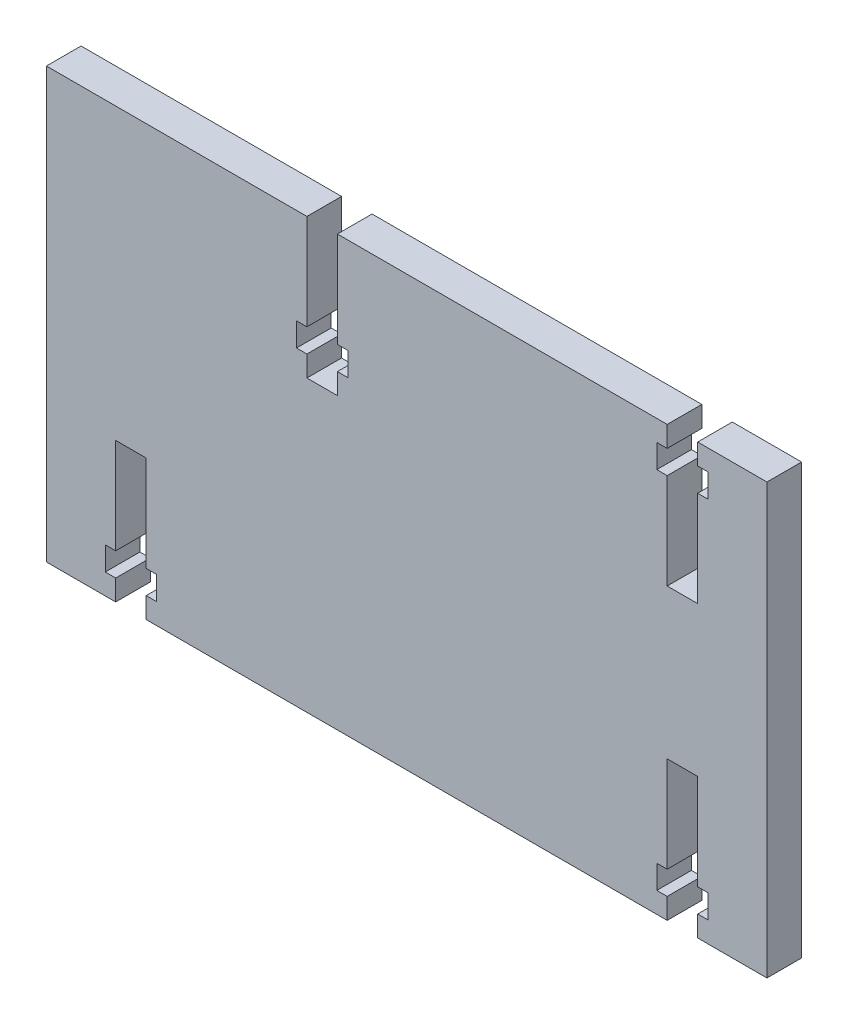
SolidWorks part; units mm, degrees
ref_plane "Front Plane" through (0, 0, 0) normal (0, 0, 1) x (1, 0, 0)
ref_plane "Top Plane" through (0, 0, 0) normal (0, 1, 0) x (1, 0, 0)
ref_plane "Right Plane" through (0, 0, 0) normal (1, 0, 0) x (0, 0, -1)
sketch "Sketch1" plane through (0, 0, 0) normal (0, 0, 1) x (1, 0, 0)
  line L1 (-52, 31) -> (52, 31)
  line L2 (-52, 31) -> (-52, -31)
  line L3 (-52, -31) -> (52, -31)
  line L4 (52, 31) -> (52, -31)
  dimension "D1" = 104
  dimension "D2" = 62
  dimension "D3" = 31
  dimension "D4" = 52
extrude "Boss-Extrude1" add sketch "Sketch1" along normal blind 5
sketch "Sketch2" plane through (0, 0, 0) normal (0, 0, -1) x (-1, 0, 0)
  line L0 (-39.8, -31) -> (-39.8, -16.1548) construction
  line L1 (-37.6, -28) -> (-37.6, -31)
  line L2 (-42, -24.6) -> (-42, -10.8)
  line L3 (-36.1, -24.6) -> (-37.6, -24.6)
  line L4 (-36.1, -28) -> (-36.1, -24.6)
  line L5 (-37.6, -28) -> (-36.1, -28)
  line L6 (-43.5, -24.6) -> (-42, -24.6)
  line L7 (-43.5, -28) -> (-43.5, -24.6)
  line L8 (-42, -28) -> (-43.5, -28)
  line L9 (-42, -31) -> (-37.6, -31)
  line L10 (-37.6, -10.8) -> (-37.6, -24.6)
  line L11 (-42, -10.8) -> (-37.6, -10.8)
  line L12 (-42, -31) -> (-42, -28)
  line L13 (52, -31) -> (-52, -31) construction
  line L14 (-52, -31) -> (-52, 31) construction
  line L15 (0, 0) -> (0, -16.1548) construction
  line L16 (0, 0) -> (21.3086, 0) construction
  line L17 (39.8, -31) -> (39.8, -16.1548) construction
  line L18 (42, -31) -> (42, -28)
  line L19 (42, -10.8) -> (37.6, -10.8)
  line L20 (37.6, -10.8) -> (37.6, -24.6)
  line L21 (42, -31) -> (37.6, -31)
  line L22 (42, -28) -> (43.5, -28)
  line L23 (43.5, -28) -> (43.5, -24.6)
  line L24 (43.5, -24.6) -> (42, -24.6)
  line L25 (37.6, -28) -> (36.1, -28)
  line L26 (36.1, -28) -> (36.1, -24.6)
  line L27 (36.1, -24.6) -> (37.6, -24.6)
  line L28 (42, -24.6) -> (42, -10.8)
  line L29 (37.6, -28) -> (37.6, -31)
  line L30 (12.2, 10.8) -> (12.2, 25.6452) construction
  line L43 (-39.8, 31) -> (-39.8, 16.1548) construction
  line L44 (-42, 31) -> (-42, 28)
  line L45 (-42, 10.8) -> (-37.6, 10.8)
  line L46 (-37.6, 10.8) -> (-37.6, 24.6)
  line L47 (-42, 31) -> (-37.6, 31)
  line L48 (-42, 28) -> (-43.5, 28)
  line L49 (-43.5, 28) -> (-43.5, 24.6)
  line L50 (-43.5, 24.6) -> (-42, 24.6)
  line L51 (-37.6, 28) -> (-36.1, 28)
  line L52 (-36.1, 28) -> (-36.1, 24.6)
  line L53 (-36.1, 24.6) -> (-37.6, 24.6)
  line L54 (-42, 24.6) -> (-42, 10.8)
  line L55 (-37.6, 28) -> (-37.6, 31)
  line L56 (14.4, 13.8) -> (14.4, 10.8)
  line L57 (10, 17.2) -> (10, 31)
  line L58 (15.9, 17.2) -> (14.4, 17.2)
  line L59 (15.9, 13.8) -> (15.9, 17.2)
  line L60 (14.4, 13.8) -> (15.9, 13.8)
  line L61 (8.5, 17.2) -> (10, 17.2)
  line L62 (8.5, 13.8) -> (8.5, 17.2)
  line L63 (10, 13.8) -> (8.5, 13.8)
  line L64 (10, 10.8) -> (14.4, 10.8)
  line L65 (14.4, 31) -> (14.4, 17.2)
  line L66 (10, 31) -> (14.4, 31)
  line L67 (10, 10.8) -> (10, 13.8)
  line L68 (-52, 31) -> (52, 31) construction
  dimension "D1" = 13.8
  dimension "D2" = 3.4
  dimension "D3" = 3
  dimension "D4" = 2.2
  dimension "D5" = 4.4
  dimension "D6" = 1.5
  dimension "D7" = 1.5
  dimension "D8" = 10
  dimension "D9" = 13.8
  dimension "D10" = 3.4
  dimension "D11" = 3
  dimension "D12" = 2.2
  dimension "D13" = 4.4
  dimension "D14" = 1.5
  dimension "D15" = 1.5
  dimension "D16" = 10
extrude "Cut-Extrude1" cut sketch "Sketch2" against normal blind 10
